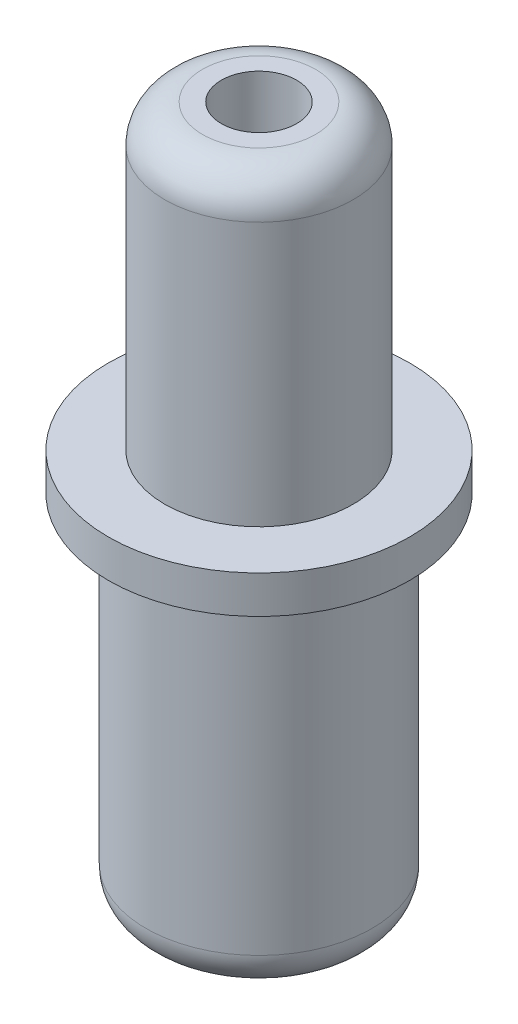
SolidWorks part; units mm, degrees
material "ABS"
ref_plane "Спереди" through (0, 0, 0) normal (0, 0, 1) x (1, 0, 0)
ref_plane "Сверху" through (0, 0, 0) normal (0, 1, 0) x (1, 0, 0)
ref_plane "Справа" through (0, 0, 0) normal (1, 0, 0) x (0, 0, -1)
sketch "Эскиз1" plane through (0, 0, 0) normal (1, 0, 0) x (0, 0, -1)
  line L0 (0, 0) -> (0, 17) construction
  line L1 (0, 0) -> (0, -1.5) construction
  line L2 (2.5, 16) -> (2.5, 9)
  line L3 (1.5, 17) -> (1, 17)
  line L4 (1, 17) -> (1, -1.5)
  line L5 (2, -1.5) -> (1, -1.5)
  line L6 (4.7, 9) -> (-4.7, 9) construction
  line L7 (2.5, 9) -> (4, 9)
  line L8 (4, 9) -> (4, 8)
  line L10 (4, 8) -> (3, 8)
  line L12 (3, 8) -> (3, -0.5)
  arc A0 (2, -1.5) -> (3, -0.5) centre (2, -0.5) ccw
  arc A1 (1.5, 17) -> (2.5, 16) centre (1.5, 16) cw
  dimension "D9" = 1
  dimension "D1" = 17
  dimension "D2" = 1.5
  dimension "D3" = 6
  dimension "D4" = 2
  dimension "D5" = 5
  dimension "D6" = 8
  dimension "D7" = 18.5
  dimension "D8" = 1
revolve "Повернуть1" add sketch "Эскиз1" angle 360 about L0
